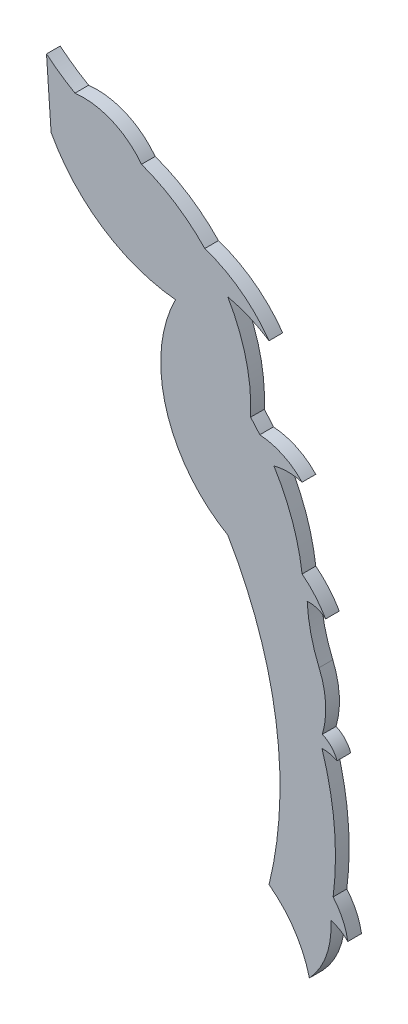
SolidWorks part; units mm, degrees
ref_plane "Front Plane" through (0, 0, 0) normal (0, 0, 1) x (1, 0, 0)
ref_plane "Top Plane" through (0, 0, 0) normal (0, 1, 0) x (1, 0, 0)
ref_plane "Right Plane" through (0, 0, 0) normal (1, 0, 0) x (0, 0, -1)
sketch "Sketch1" plane through (0, 0, 0) normal (0, 0, 1) x (1, 0, 0)
  line L0 (-31.663, 93.5924) -> (-27.249, 30.2932) construction
  line L1 (-31.1157, 85.743) -> (-31.626, 93.062)
  arc A0 (-31.626, 93.062) -> (-28.4568, 90.8649) centre (-17.3025, 110.3384) ccw
  arc A1 (-32.7228, 94.0334) -> (-28.4568, 90.8649) centre (-17.3025, 110.3384) ccw construction
  arc A2 (-28.4568, 90.8649) -> (-21.0423, 87.7003) centre (-27.5395, 82.7457) cw
  arc A3 (-21.0423, 87.7003) -> (-13.9945, 83.1032) centre (-27.3525, 70.325) cw
  arc A4 (-13.9945, 83.1032) -> (-6.8345, 77.7821) centre (-18.5606, 69.4816) cw
  arc A5 (-6.8345, 77.7821) -> (-11.4345, 79.7238) centre (-14.4944, 66.0552) ccw
  arc A6 (-11.4345, 79.7238) -> (-8.8911, 69.3781) centre (-27.3525, 70.325) cw
  arc A7 (-8.8911, 69.3781) -> (-7.8665, 68.1965) centre (-25.0332, 54.3458) cw
  arc A8 (-7.8665, 68.1965) -> (-3.1507, 65.9768) centre (-8.3342, 61.0837) cw
  arc A9 (-3.1507, 65.9768) -> (-6.2914, 65.9768) centre (-4.721, 60.2455) ccw
  arc A10 (-6.2914, 65.9768) -> (-3.1507, 57.1195) centre (-25.0332, 54.3458) cw
  arc A11 (-3.1507, 57.1195) -> (-0.532, 54.0907) centre (-9.6432, 48.8594) cw
  arc A12 (-0.532, 54.0907) -> (-2.5844, 54.7666) centre (-2.3132, 52.1359) ccw
  arc A13 (-2.5844, 54.7666) -> (-2.1746, 51.8399) centre (14.2046, 55.6257) ccw
  arc A14 (-2.5844, 54.7666) -> (-1.2585, 49.0301) centre (14.2046, 55.6257) ccw construction
  arc A15 (-2.1746, 51.8399) -> (-1.2585, 49.0301) centre (14.2046, 55.6257) ccw
  arc A16 (-1.2585, 49.0301) -> (-0.8934, 42.7819) centre (-9.7746, 45.3977) cw
  arc A17 (-0.8934, 42.7819) -> (0.7427, 41.0491) centre (-2.1274, 39.978) cw
  arc A18 (0.7427, 41.0491) -> (-0.9411, 41.4095) centre (-0.8934, 37.5182) ccw
  arc A19 (-0.9411, 41.4095) -> (0.3039, 27.692) centre (-31.0649, 31.7602) cw
  arc A20 (0.3039, 27.692) -> (1.9407, 24.2088) centre (-5.0791, 23.0362) cw
  arc A21 (1.9407, 24.2088) -> (0.0487, 25.312) centre (-1.0186, 21.3076) ccw
  arc A22 (0.0487, 25.312) -> (-2.3394, 18.5502) centre (-8.8911, 24.6667) cw
  arc A23 (-2.3394, 18.5502) -> (-6.8345, 25.312) centre (-13.9945, 15.6771) ccw
  arc A24 (-6.8345, 25.312) -> (-11.4345, 56.7378) centre (-47.7068, 35.3789) ccw
  arc A25 (-11.4345, 56.7378) -> (-17.2533, 76.5309) centre (-3.9075, 69.7024) cw
  arc A26 (-17.2533, 76.5309) -> (-31.1157, 85.743) centre (-15.5365, 94.1503) cw
extrude "Boss-Extrude1" add sketch "Sketch1" along normal blind 1.524
